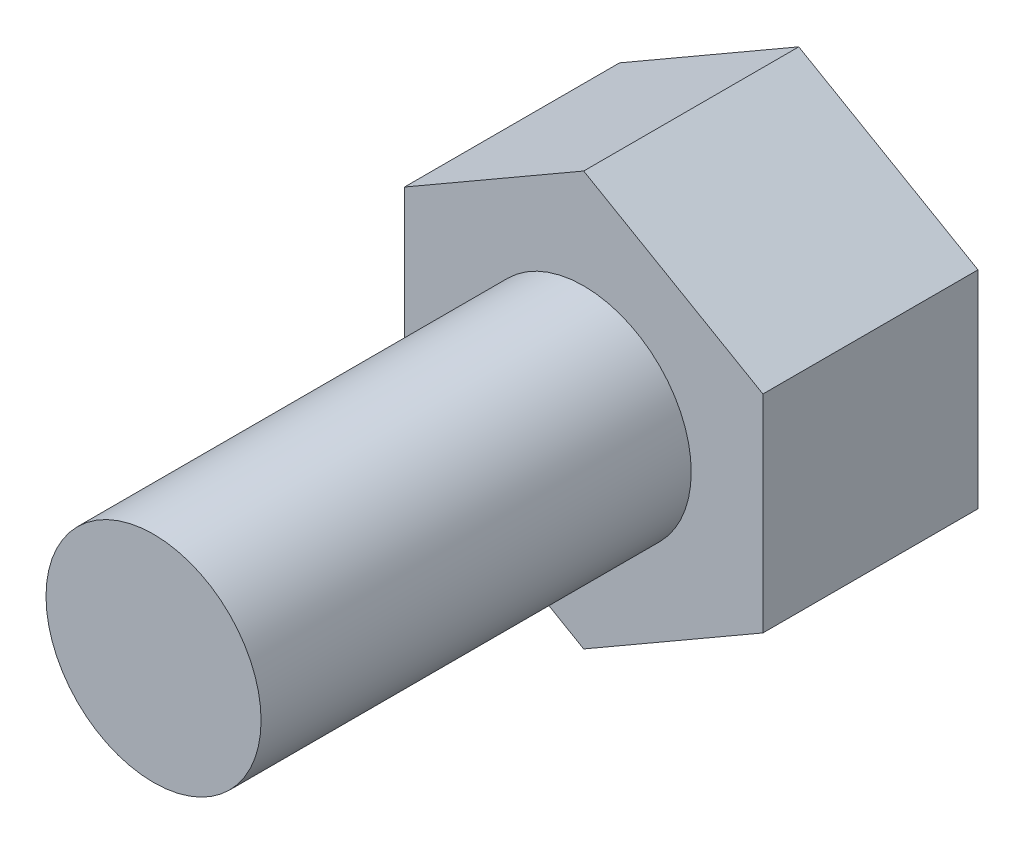
SolidWorks part; units mm, degrees
ref_plane "Front Plane" through (0, 0, 0) normal (0, 0, 1) x (1, 0, 0)
ref_plane "Top Plane" through (0, 0, 0) normal (0, 1, 0) x (1, 0, 0)
ref_plane "Right Plane" through (0, 0, 0) normal (1, 0, 0) x (0, 0, -1)
sketch "Sketch1" plane through (0, 0, 0) normal (0, 0, 1) x (1, 0, 0)
  circle A0 centre (-63.4948, 14.9787) radius 1.5
extrude "Boss-Extrude1" add sketch "Sketch1" along normal blind 6
sketch "Sketch2" plane through (0, 0, 0) normal (0, 0, -1) x (-1, 0, 0)
  line L1 (63.4948, 12.092) -> (65.9948, 13.5353)
  line L2 (65.9948, 13.5353) -> (65.9948, 16.4221)
  line L3 (65.9948, 16.4221) -> (63.4948, 17.8655)
  line L4 (63.4948, 17.8655) -> (60.9948, 16.4221)
  line L5 (60.9948, 16.4221) -> (60.9948, 13.5353)
  line L6 (60.9948, 13.5353) -> (63.4948, 12.092)
  circle A0 centre (63.4948, 14.9787) radius 2.5 construction
  dimension "D1" = 5
extrude "Boss-Extrude2" add sketch "Sketch2" along normal blind 3
